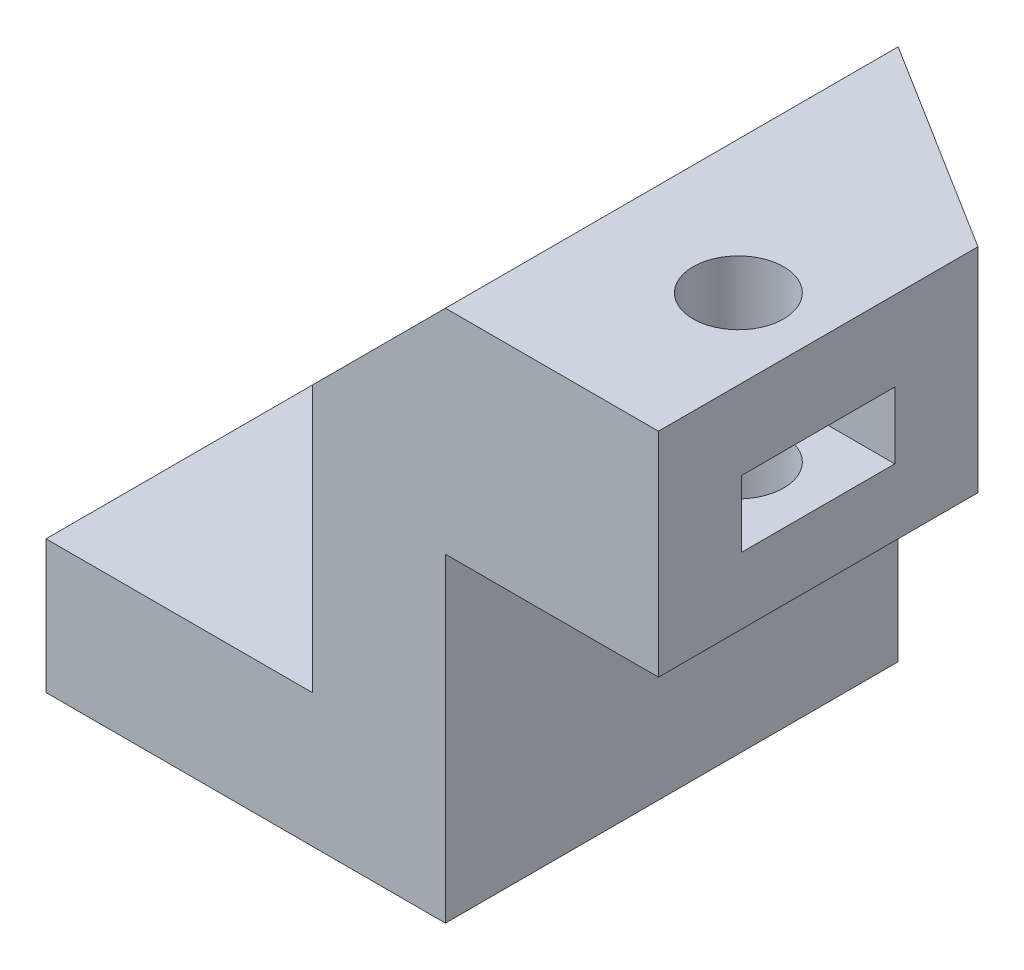
SolidWorks part; units mm, degrees
ref_plane "Plano frontal" through (0, 0, 0) normal (0, 0, 1) x (1, 0, 0)
ref_plane "Plano superior" through (0, 0, 0) normal (0, 1, 0) x (1, 0, 0)
ref_plane "Plano direito" through (0, 0, 0) normal (1, 0, 0) x (0, 0, -1)
sketch "Esboço1" plane through (0, 0, 0) normal (0, 0, 1) x (1, 0, 0)
  line L0 (0, 0) -> (15, 0)
  line L1 (15, 0) -> (15, 12)
  line L2 (15, 12) -> (23, 12)
  line L3 (23, 12) -> (23, 20)
  line L4 (23, 20) -> (15, 20)
  line L5 (15, 20) -> (10, 15)
  line L6 (10, 15) -> (10, 5)
  line L7 (10, 5) -> (0, 5)
  line L8 (0, 5) -> (0, 0)
  dimension "D1" = 5
  dimension "D2" = 15
  dimension "D3" = 12
  dimension "D4" = 8
  dimension "D5" = 8
  dimension "D6" = 5
  dimension "D7" = 8
  dimension "D8" = 135
extrude "Ressalto-extrusão1" add sketch "Esboço1" against normal blind 17 contours L5 L6 L7 L8 L0 L1 L2 L3 L4
sketch "Esboço2" plane through (0, 5, 0) normal (0, 1, 0) x (1, 0, 0)
  line L0 (10, 0) -> (0, 0) construction
  line L3 (5, 0) -> (5, 17) construction
  line L4 (10, 17) -> (0, 17) construction
  circle A0 centre (5, 10) radius 2.6
  dimension "D1" = 5.2
  dimension "D2" = 10
extrude "Corte-extrusão1" cut sketch "Esboço2" against normal blind 20
chamfer "Chanfro1" distance 8 distance2 5 1 edges at (23, 16, -17)
sketch "Esboço3" plane through (0, 20, 0) normal (0, 1, 0) x (1, 0, 0)
  line L0 (23, 12) -> (23, 0) construction
  line L1 (23, 6) -> (15, 6) construction
  line L2 (15, 17) -> (15, 0) construction
  circle A0 centre (20, 6) radius 1.7
  dimension "D1" = 3.4
  dimension "D2" = 3
extrude "Corte-extrusão2" cut sketch "Esboço3" against normal through all
sketch "Esboço4" plane through (0, 20, 0) normal (0, 1, 0) x (1, 0, 0)
  line L0 (23, 12) -> (23, 0) construction
  line L3 (23, 8.875) -> (18.3401, 8.875)
  line L4 (18.3401, 8.875) -> (16.6802, 6)
  line L5 (16.6802, 6) -> (18.3401, 3.125)
  line L6 (18.3401, 3.125) -> (23, 3.125)
  line L7 (23, 8.875) -> (23, 3.125)
  line L8 (23, 6.5538) -> (22.4898, 7.4375) [skipped]
  line L9 (21.6599, 3.125) -> (22.4898, 4.5625) [skipped]
  circle A0 centre (20, 6) radius 2.875 construction
  dimension "D1" = 5.75
extrude "Corte-extrusão3" cut sketch "Esboço4" against normal blind 2.5 from offset 3
